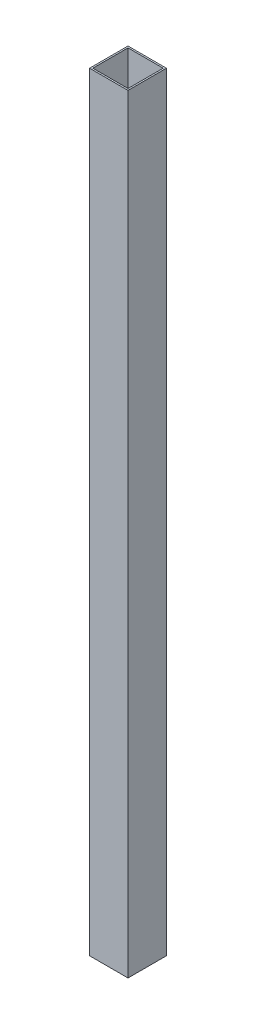
SolidWorks part; units mm, degrees
ref_plane "Front Plane" through (0, 0, 0) normal (0, 0, 1) x (1, 0, 0)
ref_plane "Top Plane" through (0, 0, 0) normal (0, 1, 0) x (1, 0, 0)
ref_plane "Right Plane" through (0, 0, 0) normal (1, 0, 0) x (0, 0, -1)
sketch "Sketch1" plane through (0, 0, 0) normal (0, 1, 0) x (1, 0, 0)
  line L1 (0, 0) -> (38.1, 0)
  line L2 (0, 0) -> (0, 38.1)
  line L3 (0, 38.1) -> (38.1, 38.1)
  line L4 (38.1, 0) -> (38.1, 38.1)
  line L5 (1.6002, 36.4998) -> (36.4998, 36.4998)
  line L6 (1.6002, 36.4998) -> (1.6002, 1.6002)
  line L7 (1.6002, 1.6002) -> (36.4998, 1.6002)
  line L8 (36.4998, 36.4998) -> (36.4998, 1.6002)
  dimension "D1" = 1.6002
  dimension "D2" = 1.6002
  dimension "D3" = 1.6002
  dimension "D4" = 1.6002
  dimension "D5" = 38.1
  dimension "D6" = 38.1
extrude "Boss-Extrude1" add sketch "Sketch1" along normal blind 762
